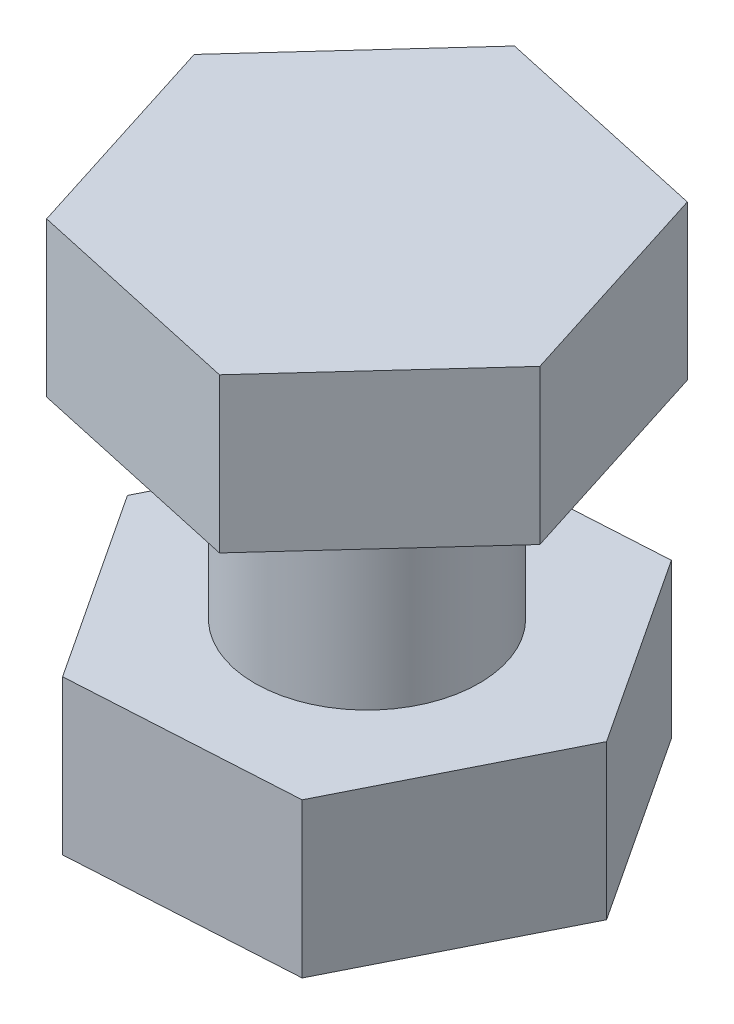
SolidWorks part; units mm, degrees
ref_plane "Front Plane" through (0, 0, 0) normal (0, 0, 1) x (1, 0, 0)
ref_plane "Top Plane" through (0, 0, 0) normal (0, 1, 0) x (1, 0, 0)
ref_plane "Right Plane" through (0, 0, 0) normal (1, 0, 0) x (0, 0, -1)
sketch "Sketch1" plane through (0, 0, 0) normal (0, 1, 0) x (1, 0, 0)
  circle A0 centre (0, 0) radius 3.175
  dimension "D1" = 6.35
extrude "Boss-Extrude1" add sketch "Sketch1" along normal blind 10
sketch "Sketch2" plane through (0, 0, 0) normal (0, -1, 0) x (1, 0, 0)
  line L1 (6.4049, -0.3731) -> (3.5256, 5.3603)
  line L2 (3.5256, 5.3603) -> (-2.8794, 5.7334)
  line L3 (-2.8794, 5.7334) -> (-6.4049, 0.3731)
  line L4 (-6.4049, 0.3731) -> (-3.5256, -5.3603)
  line L5 (-3.5256, -5.3603) -> (2.8794, -5.7334)
  line L6 (2.8794, -5.7334) -> (6.4049, -0.3731)
  circle A0 centre (0, 0) radius 5.5563 construction
  dimension "D1" = 11.1125
extrude "Boss-Extrude2" add sketch "Sketch2" along normal blind 4.3656
sketch "Sketch3" plane through (0, 10, 0) normal (0, 1, 0) x (1, 0, 0)
  line L1 (-6.2665, 1.376) -> (-4.3249, -4.739)
  line L2 (-4.3249, -4.739) -> (1.9416, -6.115)
  line L3 (1.9416, -6.115) -> (6.2665, -1.376)
  line L4 (6.2665, -1.376) -> (4.3249, 4.739)
  line L5 (4.3249, 4.739) -> (-1.9416, 6.115)
  line L6 (-1.9416, 6.115) -> (-6.2665, 1.376)
  circle A0 centre (0, 0) radius 5.5562 construction
  dimension "D1" = 11.1125
extrude "Boss-Extrude3" add sketch "Sketch3" against normal blind 4.3656
